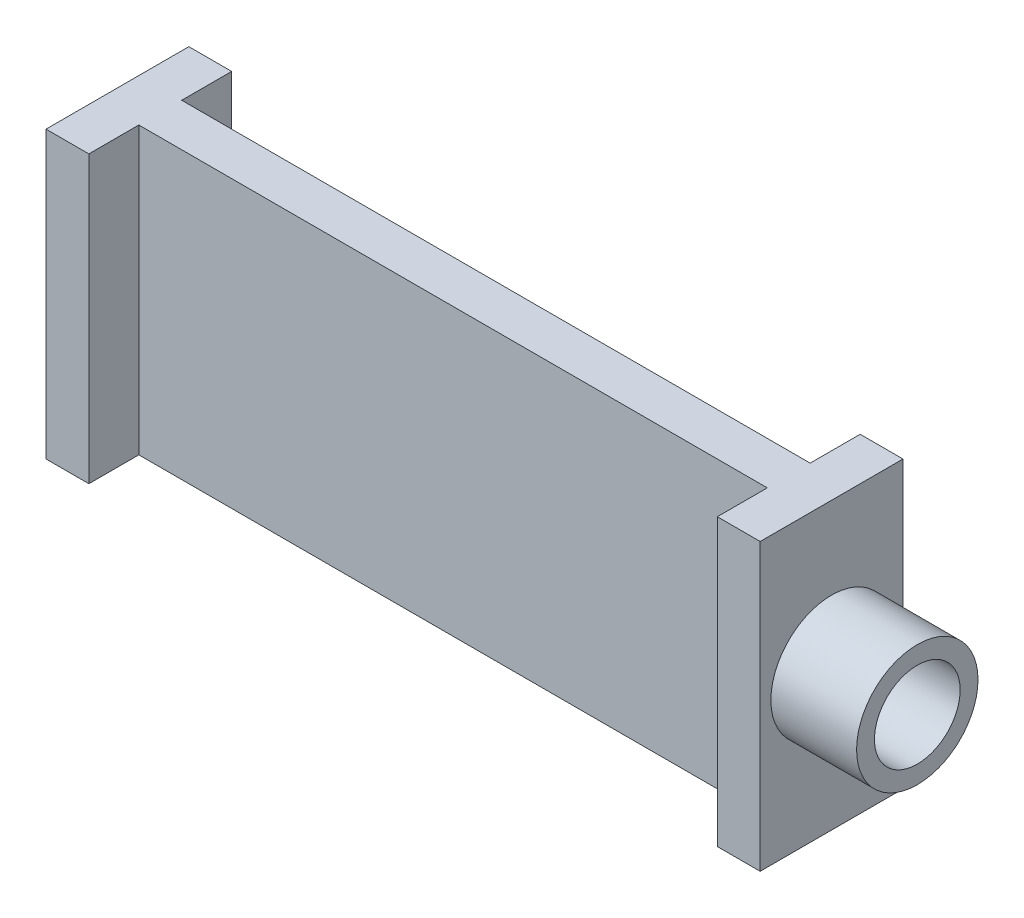
SolidWorks part; units mm, degrees
ref_plane "Front Plane" through (0, 0, 0) normal (0, 0, 1) x (1, 0, 0)
ref_plane "Top Plane" through (0, 0, 0) normal (0, 1, 0) x (1, 0, 0)
ref_plane "Right Plane" through (0, 0, 0) normal (1, 0, 0) x (0, 0, -1)
sketch "Sketch1" plane through (0, 0, 0) normal (0, 1, 0) x (1, 0, 0)
  line L0 (0, 0) -> (0, 20)
  line L1 (0, 20) -> (6, 20)
  line L2 (6, 20) -> (6, 13)
  line L3 (6, 13) -> (94, 13)
  line L4 (94, 13) -> (94, 20)
  line L5 (94, 20) -> (100, 20)
  line L6 (100, 20) -> (100, 0)
  line L7 (100, 0) -> (94, 0)
  line L8 (94, 0) -> (94, 7)
  line L9 (94, 7) -> (6, 7)
  line L10 (6, 7) -> (6, 0)
  line L11 (6, 0) -> (0, 0)
  line L12 (0, 10) -> (100, 10) construction
  point P9 (6, 16.5)
  dimension "D1" = 6
  dimension "D2" = 6
  dimension "D3" = 6
  dimension "D4" = 20
  dimension "D5" = 100
extrude "Body" add sketch "Sketch1" along normal blind 40
sketch "Sketch2" plane through (100, 0, 0) normal (1, 0, 0) x (0, 0, -1)
  line L0 (0, 40) -> (20, 0) construction
  circle A0 centre (10, 20) radius 8.5
  circle A1 centre (10, 20) radius 6
  dimension "D1" = 17
  dimension "D2" = 12
extrude "Nozzle" add sketch "Sketch2" along normal blind 12
ref_plane "Center Plane zx" through (0, 20, 0) normal (0, 1, 0) x (1, 0, 0)
ref_plane "Center Plane yz" through (50, 0, 0) normal (1, 0, 0) x (0, 0, -1)
sketch "Alignment: Center Line" plane through (0, 20, 0) normal (0, 1, 0) x (1, 0, 0)
  line L0 (0, 10) -> (112, 10) construction
  line L1 (0, 20) -> (0, 0) construction
  line L2 (112, 1.5) -> (112, 18.5) construction
sketch "Alignment: yz" plane through (50, 0, 0) normal (1, 0, 0) x (0, 0, -1)
  circle A0 centre (10, 20) radius 15 construction
  circle A1 centre (10, 35) radius 1.6 construction
  circle A2 centre (25, 20) radius 1.6 construction
  circle A3 centre (10, 5) radius 1.6 construction
  circle A4 centre (-5, 20) radius 1.6 construction
  point P14 (10, 20)
  dimension "D1" = 30
  dimension "D2" = 3.2
  dimension "D3" = 4
equation "\"Length\"= 100mm"
equation "\"Width\"= 40mm"
equation "\"Height\"= 20mm"
equation "\"D1@Center Plane zx\" = \"Width\" / 2"
equation "\"D1@Center Plane yz\"=\"Length\"/2"
